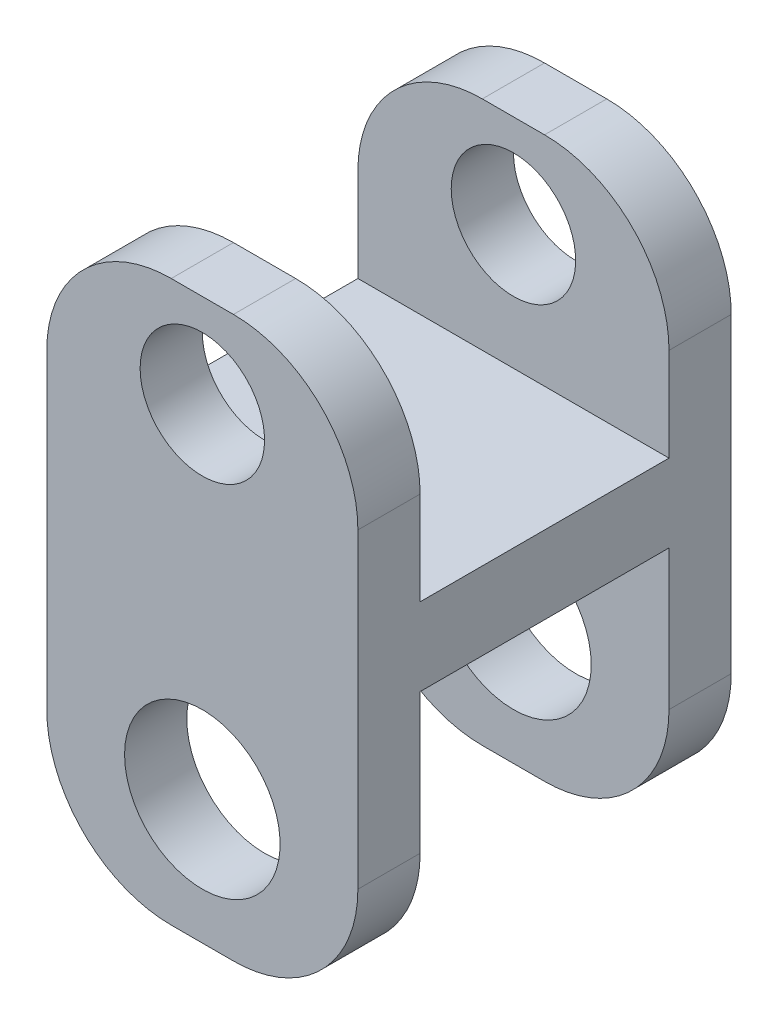
SolidWorks part; units mm, degrees
ref_plane "Alzado" through (0, 0, 0) normal (0, 0, 1) x (1, 0, 0)
ref_plane "Planta" through (0, 0, 0) normal (0, 1, 0) x (1, 0, 0)
ref_plane "Vista lateral" through (0, 0, 0) normal (1, 0, 0) x (0, 0, -1)
sketch "Croquis1" plane through (0, 0, 0) normal (1, 0, 0) x (0, 0, -1)
  line L0 (4, 9) -> (6, 9)
  line L1 (-6, -9) -> (-4, -9)
  line L2 (-6, -9) -> (-6, 9)
  line L3 (-6, 9) -> (-4, 9)
  line L4 (6, -9) -> (6, 9)
  line L5 (-6, -9) -> (6, 9) construction
  line L6 (-6, 9) -> (6, -9) construction
  line L8 (-4, 9) -> (-4, 2)
  line L9 (-4, 2) -> (4, 2)
  line L10 (4, 9) -> (4, 2)
  line L12 (-4, -9) -> (-4, -0.5)
  line L13 (-4, -0.5) -> (4, -0.5)
  line L14 (4, -9) -> (4, -0.5)
  line L15 (4, -9) -> (6, -9)
  point P0 (0, 0)
  dimension "D1" = 12
  dimension "D2" = 18
  dimension "D3" = 7
  dimension "D4" = 2
  dimension "D5" = 2
  dimension "D6" = 2.5
  dimension "D7" = 2
  dimension "D8" = 2
extrude "Saliente-Extruir1" add sketch "Croquis1" along normal mid plane 10
sketch "Croquis2" plane through (0, 0, -6) normal (0, 0, -1) x (-1, 0, 0)
  line L0 (-5, 0) -> (-5, 9) construction
  line L1 (-5, -9) -> (-5, 9) construction
  line L2 (-5, 1) -> (5, 1) construction
  line L3 (5, -9) -> (5, 9) construction
  line L4 (-5, 9) -> (5, 9) construction
  line L5 (0, 9) -> (0, 6) construction
  line L6 (0, -9) -> (0, -5) construction
  line L7 (-5, -9) -> (5, -9) construction
  circle A1 centre (0, 6) radius 2
  circle A2 centre (0, -5) radius 2.5
  dimension "D2" = 4
  dimension "D4" = 5
  dimension "D5" = 4
  dimension "D1" = 8
  dimension "D3" = 3
extrude "Cortar-Extruir1" cut sketch "Croquis2" against normal blind 12
fillet "Redondeo1" radius 4 8 edges at (-5, 9, 5) (-5, 9, -5) (5, 9, 5) (5, 9, -5) (5, -9, 5) (-5, -9, 5) (-5, -9, -5) (5, -9, -5)
